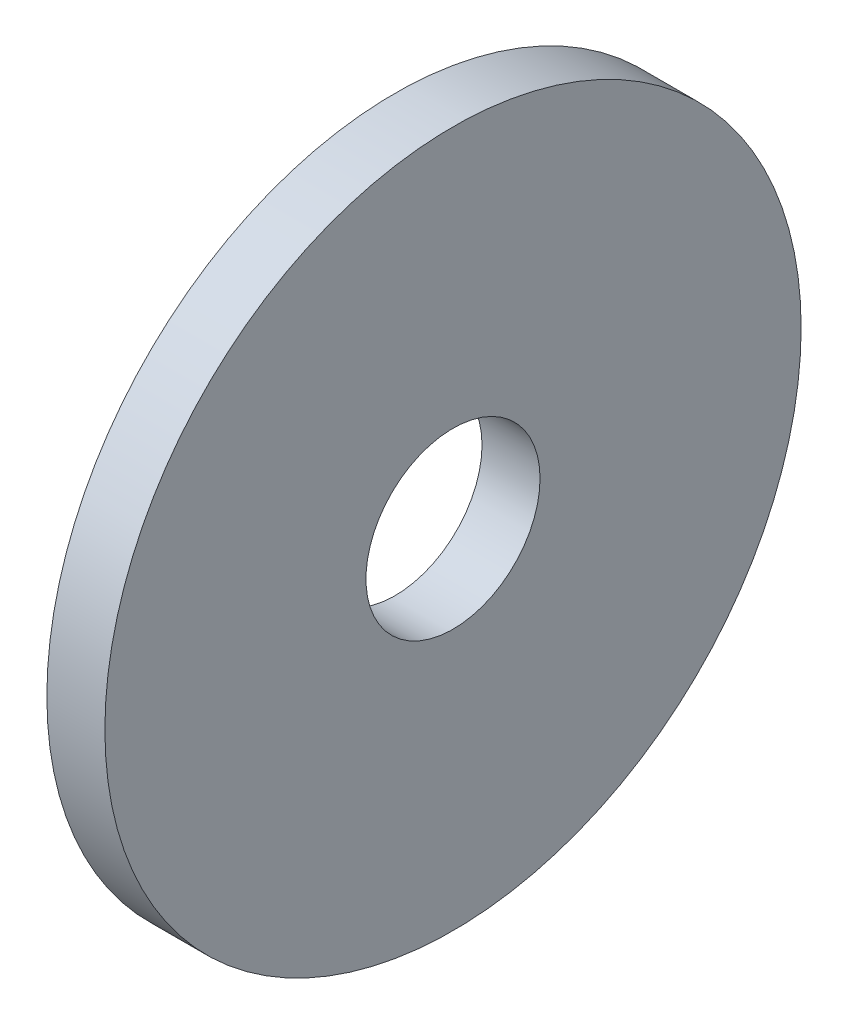
SolidWorks part; units mm, degrees
material "Acrylic (Medium-high impact)"
ref_plane "Front Plane" through (0, 0, 0) normal (0, 0, 1) x (1, 0, 0)
ref_plane "Top Plane" through (0, 0, 0) normal (0, 1, 0) x (1, 0, 0)
ref_plane "Right Plane" through (0, 0, 0) normal (1, 0, 0) x (0, 0, -1)
sketch "Sketch1" plane through (0, 0, 0) normal (1, 0, 0) x (0, 0, -1)
  circle A0 centre (0, 0) radius 12
  dimension "D1" = 24
extrude "Boss-Extrude1" add sketch "Sketch1" along normal blind 2
sketch "Sketch2" plane through (2, 0, 0) normal (1, 0, 0) x (0, 0, -1)
  circle A0 centre (0, 0) radius 3
  dimension "D1" = 6
extrude "Cut-Extrude1" cut sketch "Sketch2" against normal through all and the other way through all
